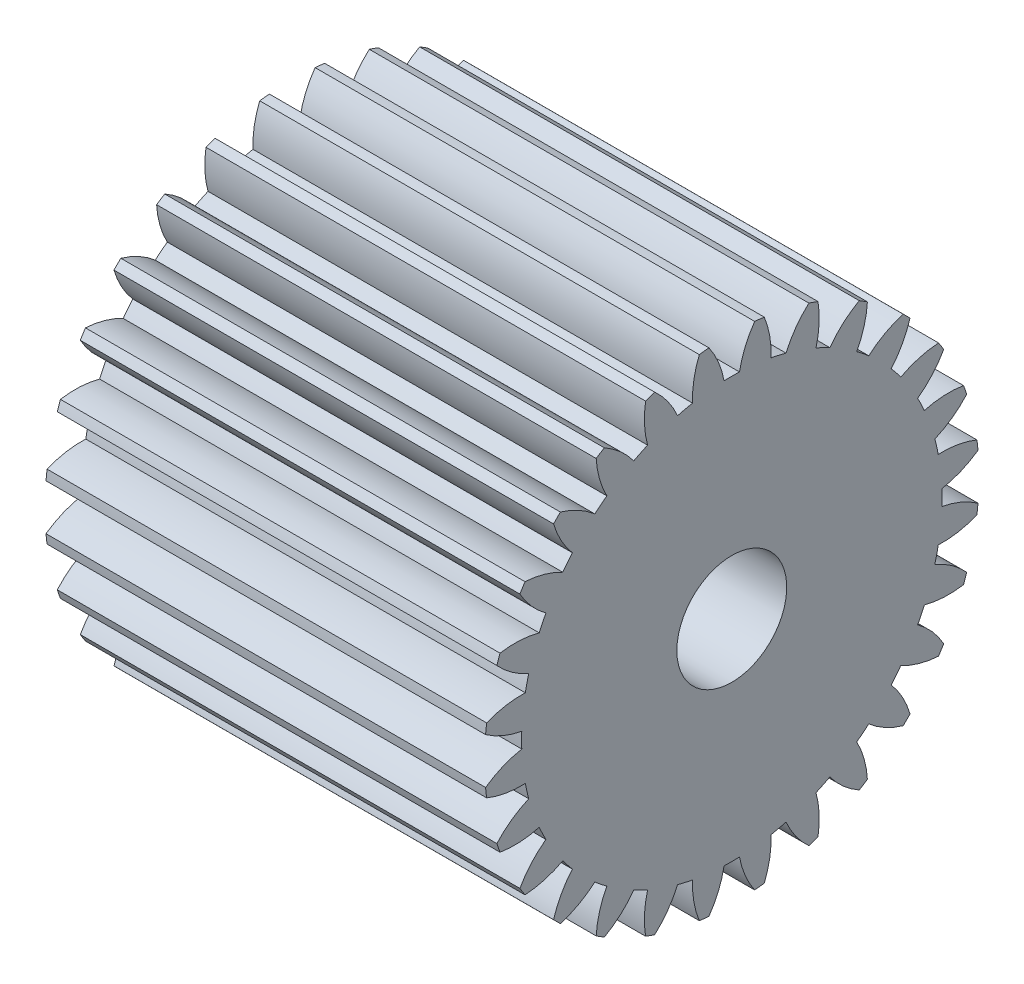
SolidWorks part; units mm, degrees
ref_plane "Plane1" through (0, 0, 0) normal (0, 0, 1) x (1, 0, 0)
ref_plane "Plane2" through (0, 0, 0) normal (0, 1, 0) x (1, 0, 0)
ref_plane "Plane3" through (0, 0, 0) normal (1, 0, 0) x (0, 0, -1)
other "Configuration Table"
sketch "HoldingSke" plane through (0, 0, 0) normal (0, 1, 0) x (1, 0, 0)
  line L0 (0, 0) -> (0.5886, -0.313)
  line L1 (-15, 0) -> (100, 0) construction
  line L2 (0, 0) -> (-2.1039, 2.3779)
  line L3 (0, 0) -> (-11.863, 4.5341)
  line L4 (0, 0) -> (7.6251, 4.0544)
  line L5 (0, 0) -> (-46.8476, -17.4728)
  line L6 (0, 0) -> (-33.1585, -22.3721)
  line L7 (-2.1039, 2.3779) -> (8.6586, 51.2059)
  line L8 (-76.2, 54.61) -> (-74.4, 54.61)
  line L9 (-71.009, 38.7566) -> (-53.1078, 45.2721)
  line L10 (-76.2, 71.12) -> (104.1128, 71.12)
  line L11 (0, 0) -> (-40, 0)
  line L12 (-76.2, 101.6) -> (-76.147, 101.6)
  line L13 (24.9733, 27.94) -> (52.9518, 28.4284)
  line L14 (24.9733, 27.94) -> (24.9743, 27.94)
  line L15 (24.9733, 27.94) -> (100.4006, 29.5858)
  line L16 (-63.627, -1.5) -> (-12.827, -1.5)
  circle A0 centre (0, 0) radius 5
  circle A1 centre (0, 0) radius 19.124
  circle A2 centre (0, 0) radius 37.5
  circle A3 centre (0, 0) radius 5
  dimension "MHD" = 38.248
  dimension "Hub_dia" = 75
  dimension "Bore" = 10
  dimension "MBD" = 10
  dimension "Num_teeth" = 28
  dimension "Pitch" = 0.6667
  dimension "Overall_len" = 50
  dimension "Show_teeth" = 28
  dimension "Thickness" = 40
  dimension "OAL" = 50.0001
  dimension "T_dim" = 1.8
  dimension "Ap" = 20
  dimension "H" = 19.05
  dimension "Pitch_radius" = 180.3128
  dimension "Width" = 40
  dimension "Backlash" = 0.053
  dimension "Addendum_fac" = 1
  dimension "Dedendum_fac" = 1.25
  dimension "Clearance_fac" = 0.25
  dimension "Dedendum_add" = 0.001
  dimension "Module" = 1.5
sketch "BasProSke" plane through (0, 0, 0) normal (0, 1, 0) x (1, 0, 0)
  line L0 (-10, 0) -> (60, 0) construction
  line L1 (0, 0) -> (0, 22.5)
  line L2 (0, 0) -> (40, 0)
  line L3 (40, 0) -> (40, 22.5)
  line L4 (40, 22.5) -> (0, 22.5)
  dimension "Thickness" = 40
  dimension "Diameter" = 45
revolve "Base-Revolve" add sketch "BasProSke" angle 360 about L0
sketch "TooCutSke" plane through (0, 0, 0) normal (1, 0, 0) x (0, 0, -1)
  line L1 (0, 0) -> (0, 107) construction
  line L2 (0, 0) -> (-1.2702, 20.9615) construction
  line L3 (0, 0) -> (-4.6962, 41.6802) construction
  line L4 (-1.2702, 20.9615) -> (-2.3481, 20.8401) construction
  arc A0 (0.7007, 19.1112) -> (-0.7007, 19.1112) centre (0, 0) ccw
  arc A1 (2.0988, 22.4274) -> (-2.0988, 22.4274) centre (0, 0) ccw
  circle A2 centre (0, 0) radius 21 construction
  circle A3 centre (0, 0) radius 19.7335 construction
  arc A4 (-0.7007, 19.1112) -> (-2.0988, 22.4274) centre (-8.9603, 17.5819) ccw
  arc A5 (2.0988, 22.4274) -> (0.7007, 19.1112) centre (8.9603, 17.5819) ccw
  dimension "Root_dia" = 38.248
  dimension "Overcut_dia" = 45.0508
  dimension "Pitch_dia" = 42
  dimension "Base_dia" = 39.4671
  dimension "Flank_rad" = 8.4
  dimension "Half_ang" = 6.429
  dimension "Half_CT" = 1.0847
extrude "ToothCut" cut sketch "TooCutSke" along normal through all
fillet "Breaks" [suppressed] radius 0.03
fillet "RootFillets" [suppressed] radius 0.376
pattern_circular "TeethCuts" count 28 every 12.857 about axis through (-10, 0, 0) along (1, 0, 0) of "ToothCut", "RootFillets", "Breaks"
sketch "HubNeaOneSke" plane through (0, 0, 0) normal (-1, 0, 0) x (0, 0, 1)
  circle A0 centre (0, 0) radius 19.124
  dimension "Diameter" = 38.248
extrude "HubNearOne" [suppressed] add sketch "HubNeaOneSke" along normal blind 10.0001
sketch "HubNeaBotSke" plane through (0, 0, 0) normal (-1, 0, 0) x (0, 0, 1)
  circle A0 centre (0, 0) radius 19.124
  dimension "Diameter" = 38.248
extrude "HubNearBoth" [suppressed] add sketch "HubNeaBotSke" along normal blind 5
ref_plane "FarPln" through (40, 0, 0) normal (1, 0, 0) x (0, 0, -1)
sketch "HubFarSke" plane through (40, 0, 0) normal (1, 0, 0) x (0, 0, -1)
  circle A0 centre (0, 0) radius 19.124
  dimension "Diameter" = 38.248
extrude "HubFar" [suppressed] add sketch "HubFarSke" along normal blind 5
sketch "BorSke" plane through (0, 0, 0) normal (1, 0, 0) x (0, 0, -1)
  circle A0 centre (0, 0) radius 5
  dimension "Diameter" = 10
extrude "Bore" cut sketch "BorSke" along normal mid plane 100.0001
sketch "KeySke" plane through (0, 0, 0) normal (1, 0, 0) x (0, 0, -1)
  line L0 (-2, 0) -> (-2, 6.8)
  line L1 (-2, 6.8) -> (2, 6.8)
  line L2 (2, 6.8) -> (2, 0)
  line L3 (0, 0) -> (0, 34) construction
  line L4 (-2, 0) -> (2, 0)
  dimension "Offset" = 6.8
extrude "Keyway" [suppressed] cut sketch "KeySke" along normal mid plane 100.0001
pattern_circular "Keyway2" [suppressed] count 2 every 90 about axis through (-10, 0, 0) along (1, 0, 0)
scale "Scale1" bodies to scale 103 scale about origin uniform scaling yes scale factor 2
equation "' \"Module@HoldingSke\" = 6.35"
equation "' \"Num_teeth@HoldingSke\" = 12"
equation "' \"Ap@HoldingSke\" =  20"
equation "' \"Ap@HoldingSke\" = 20"
equation "' \"Width@HoldingSke\" = 0.5 * 25.4"
equation "' \"Hub_dia@HoldingSke\"= 1 * 25.4"
equation "' \"Hub_dia@HoldingSke\" = 1 * 25.4"
equation "' \"Overall_len@HoldingSke\" = 1.0 * 25.4"
equation "' \"Bore@HoldingSke\" = 0.75 * 25.4"
equation "' \"T_dim@HoldingSke\" = 0.1 * 25.4"
equation "' \"Width@KeySke\" = 0.25 * 25.4"
equation "' \"Show_teeth@HoldingSke\" = 13"
equation "' \"Backlash@HoldingSke\" = 0.009 * 25.4"
equation "' \"Addendum_fac@HoldingSke\" = 1.0"
equation "' \"Dedendum_fac@HoldingSke\" = 1.25"
equation "' \"Dedendum_add@HoldingSke\" = 0.00005 * 25.4"
equation "' \"Clearance_fac@HoldingSke\" = 0.25"
equation "\"Pitch@HoldingSke\" = 1 / \"Module@HoldingSke\""
equation "\"Overcut_dia@TooCutSke\" = (\"Num_teeth@HoldingSke\" + 2 * \"Addendum_fac@HoldingSke\") / \"Pitch@HoldingSke\" + 0.002 * 25.4"
equation "\"Pitch_dia@TooCutSke\" = \"Num_teeth@HoldingSke\" / \"Pitch@HoldingSke\""
equation "\"Base_dia@TooCutSke\" = \"Num_teeth@HoldingSke\" / \"Pitch@HoldingSke\" * cos((\"Ap@HoldingSke\"  * 3.14159265 / 180))"
equation "\"Root_dia@TooCutSke\" = (\"Num_teeth@HoldingSke\" + 2) / \"Pitch@HoldingSke\" - 2 * (\"Addendum_fac@HoldingSke\" + \"Dedendum_fac@HoldingSke\") / \"Pitch@HoldingSke\" - \"Dedendum_add@HoldingSke\" * 2"
equation "\"Half_ang@TooCutSke\" = 180 / \"Num_teeth@HoldingSke\""
equation "\"Half_CT@TooCutSke\" = \"Num_teeth@HoldingSke\" / \"Pitch@HoldingSke\" * sin((3.14159265 / 2 / \"Num_teeth@HoldingSke\")) / 2 - 7 * \"Backlash@HoldingSke\" / 4"
equation "\"Flank_rad@TooCutSke\" = \"Num_teeth@HoldingSke\" / \"Pitch@HoldingSke\" / 5"
equation "\"Radius@RootFillets\" = \"Clearance_fac@HoldingSke\" / \"Pitch@HoldingSke\" + \"Dedendum_add@HoldingSke\""
equation "\"Break_rad@Breaks\" = 0.02 / \"Pitch@HoldingSke\""
equation "\"Thickness@HoldingSke\" = \"Width@HoldingSke\""
equation "\"OAL@HoldingSke\" = \"Thickness@HoldingSke\""
equation "\"MHD@HoldingSke\" = (\"Num_teeth@HoldingSke\" + 2) / \"Pitch@HoldingSke\" - 2 * (\"Addendum_fac@HoldingSke\" + \"Dedendum_fac@HoldingSke\")  / \"Pitch@HoldingSke\" - \"Dedendum_add@HoldingSke\" * 2"
equation "\"MBD@HoldingSke\" = (\"Num_teeth@HoldingSke\" + 2) / \"Pitch@HoldingSke\" - 2 * (\"Addendum_fac@HoldingSke\" + \"Dedendum_fac@HoldingSke\")  / \"Pitch@HoldingSke\" - \"Dedendum_add@HoldingSke\" * 2 - 0.002 * 25.4"
equation "\"MHD@HoldingSke\" = ((sgn( \"MHD@HoldingSke\" - \"Hub_dia@HoldingSke\" )-1)*( \"MHD@HoldingSke\" - \"Hub_dia@HoldingSke\" ))/-2+ \"Hub_dia@HoldingSke\""
equation "\"MBD@HoldingSke\" = ((sgn( \"MBD@HoldingSke\" - \"Bore@HoldingSke\" )-1)*( \"MBD@HoldingSke\" - \"Bore@HoldingSke\" ))/-2+ \"Bore@HoldingSke\""
equation "\"OAL@HoldingSke\" = ((sgn( \"OAL@HoldingSke\" - \"Overall_len@HoldingSke\" )+1)*( \"OAL@HoldingSke\" - \"Overall_len@HoldingSke\" ))/2 + \"Overall_len@HoldingSke\" + 0.000002 * 25.4"
equation "\"Num_teeth@TeethCuts\" = int( \"Show_teeth@HoldingSke\" ) + 1"
equation "\"Num_teeth@TeethCuts\" = ((sgn( \"Num_teeth@TeethCuts\" - \"Num_teeth@HoldingSke\" )-1)*( \"Num_teeth@TeethCuts\" - \"Num_teeth@HoldingSke\" ))/-2+ \"Num_teeth@HoldingSke\""
equation "\"Num_teeth@TeethCuts\" = ((sgn( \"Num_teeth@TeethCuts\" - 2.0)+1)*( \"Num_teeth@TeethCuts\" - 2.0))/2 +2.0"
equation "\"Angle@TeethCuts\" = 360.0 / \"Num_teeth@HoldingSke\""
equation "\"Diameter@BasProSke\" = (\"Num_teeth@HoldingSke\" + 2 * \"Addendum_fac@HoldingSke\") / \"Pitch@HoldingSke\""
equation "\"Thickness@BasProSke\"  = \"Thickness@HoldingSke\""
equation "' \"Fillet_rad@BasProSke\" =  \"Thickness@HoldingSke\" * 0.05"
equation "' \"Fillet_rad@BasProSke\" = \"Thickness@HoldingSke\" * 0.05"
equation "\"MHD@HoldingSke\" = ((sgn( \"MHD@HoldingSke\" - \"Root_dia@TooCutSke\" )-1)*( \"MHD@HoldingSke\" - \"Root_dia@TooCutSke\" ))/-2+ \"Root_dia@TooCutSke\""
equation "\"Diameter@HubNeaOneSke\" = \"MHD@HoldingSke\""
equation "\"Length@HubNearOne\" = \"OAL@HoldingSke\" - \"Thickness@BasProSke\""
equation "\"Diameter@HubNeaBotSke\" = \"MHD@HoldingSke\""
equation "\"Length@HubNearBoth\" = ( \"OAL@HoldingSke\" - \"Thickness@BasProSke\" ) / 2.0"
equation "\"Thickness@FarPln\" = \"Thickness@BasProSke\""
equation "\"Diameter@HubFarSke\" = \"MHD@HoldingSke\""
equation "\"Length@HubFar\" = ( \"OAL@HoldingSke\" - \"Thickness@BasProSke\" ) / 2.0"
equation "\"Diameter@BorSke\" = \"MBD@HoldingSke\""
equation "\"D1@Bore\" = \"OAL@HoldingSke\" * 2.0"
equation "\"D1@Keyway\" = \"OAL@HoldingSke\" * 2.0"
equation "\"Offset@KeySke\" = \"T_dim@HoldingSke\" + \"MBD@HoldingSke\" / 2.0"
